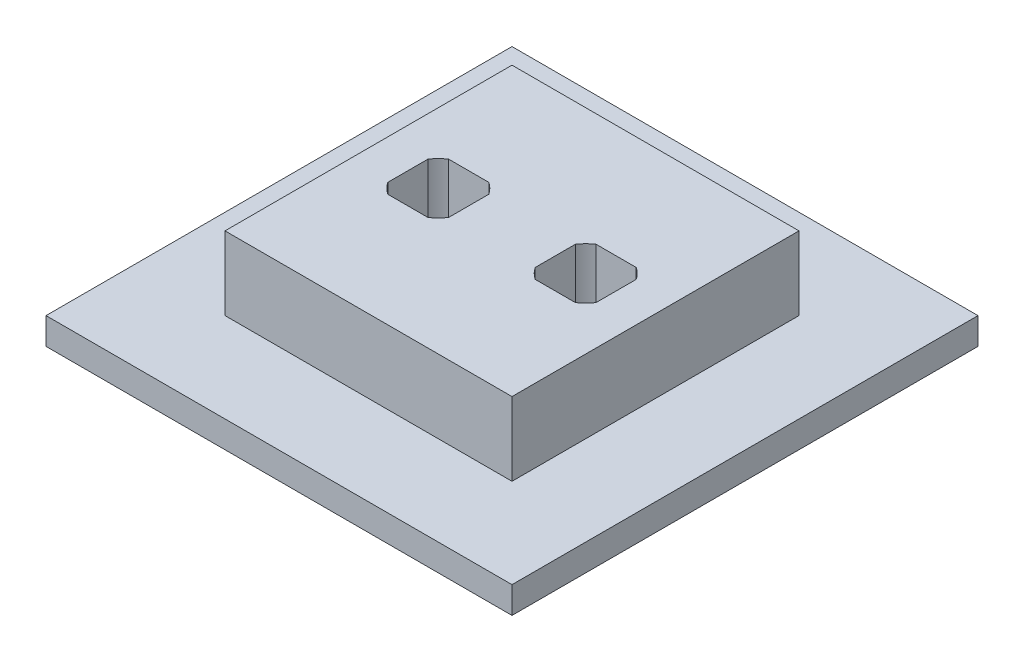
SolidWorks part; units mm, degrees
ref_plane "Front Plane" through (0, 0, 0) normal (0, 0, 1) x (1, 0, 0)
ref_plane "Top Plane" through (0, 0, 0) normal (0, 1, 0) x (1, 0, 0)
ref_plane "Right Plane" through (0, 0, 0) normal (1, 0, 0) x (0, 0, -1)
sketch "Sketch1" plane through (0, 0, 0) normal (0, 1, 0) x (1, 0, 0)
  line L1 (0, 0) -> (69.85, 0)
  line L2 (0, 0) -> (0, 69.85)
  line L3 (0, 69.85) -> (69.85, 69.85)
  line L4 (69.85, 0) -> (69.85, 69.85)
  dimension "D1" = 69.85
extrude "Boss-Extrude1" add sketch "Sketch1" along normal blind 4
sketch "Sketch2" plane through (0, 4, 0) normal (0, 1, 0) x (1, 0, 0)
  line L0 (69.85, 69.85) -> (0, 0) construction
  line L1 (13.415, 13.415) -> (56.435, 13.415)
  line L2 (13.415, 13.415) -> (13.415, 56.435)
  line L3 (13.415, 56.435) -> (56.435, 56.435)
  line L4 (56.435, 13.415) -> (56.435, 56.435)
  line L5 (13.415, 34.925) -> (56.435, 34.925) construction
  line L6 (23.876, 40.386) -> (45.974, 40.386) construction
  circle A0 centre (23.876, 34.925) radius 5.461
  circle A1 centre (45.974, 34.925) radius 5.461
  point P13 (34.925, 34.925)
  point P18 (34.925, 40.386)
  point P21 (34.925, 34.925)
  dimension "D2" = 22.098
  dimension "D1" = 10.922
  dimension "D3" = 5
extrude "Boss-Extrude2" add sketch "Sketch2" along normal blind 11
sketch "Sketch3" plane through (0, 15, 0) normal (0, 1, 0) x (1, 0, 0)
  circle A0 centre (23.876, 34.925) radius 5.461
  circle A1 centre (45.974, 34.925) radius 5.461
  circle A2 centre (23.876, 34.925) radius 5.461 construction
  circle A3 centre (45.974, 34.925) radius 5.461 construction
extrude "Cut-Extrude1" cut sketch "Sketch3" against normal through all both and the other way through all
sketch "Sketch4" plane through (0, 15, 0) normal (0, 1, 0) x (1, 0, 0)
  line L0 (56.435, 13.415) -> (56.435, 56.435) construction
  line L1 (19.315, 30.364) -> (28.437, 30.364)
  line L2 (19.315, 30.364) -> (19.315, 39.486)
  line L3 (19.315, 39.486) -> (28.437, 39.486)
  line L4 (28.437, 30.364) -> (28.437, 39.486)
  line L5 (41.413, 39.486) -> (50.535, 39.486)
  line L6 (41.413, 39.486) -> (41.413, 30.364)
  line L7 (41.413, 30.364) -> (50.535, 30.364)
  line L8 (50.535, 39.486) -> (50.535, 30.364)
  line L9 (13.415, 56.435) -> (56.435, 56.435)
  line L10 (13.415, 56.435) -> (13.415, 13.415)
  line L11 (13.415, 13.415) -> (56.435, 13.415)
  line L12 (56.435, 56.435) -> (56.435, 13.415)
  line L13 (13.415, 56.435) -> (13.415, 13.415) construction
  line L14 (56.435, 56.435) -> (13.415, 56.435) construction
  circle A1 centre (23.876, 34.925) radius 5.461 construction
  circle A2 centre (45.974, 34.925) radius 5.461 construction
  point P16 (56.435, 26.3817)
  point P19 (13.415, 45.3298)
  point P22 (56.435, 13.415)
  point P24 (13.415, 56.435)
  point P25 (13.415, 56.435)
  dimension "D1" = 0.9
  dimension "D2" = 0.9
  dimension "D3" = 0.9
  dimension "D4" = 0.9
extrude "Boss-Extrude3" add sketch "Sketch4" against normal up to surface (15 mm away) up to face at (23.876, 0, -29.464)
